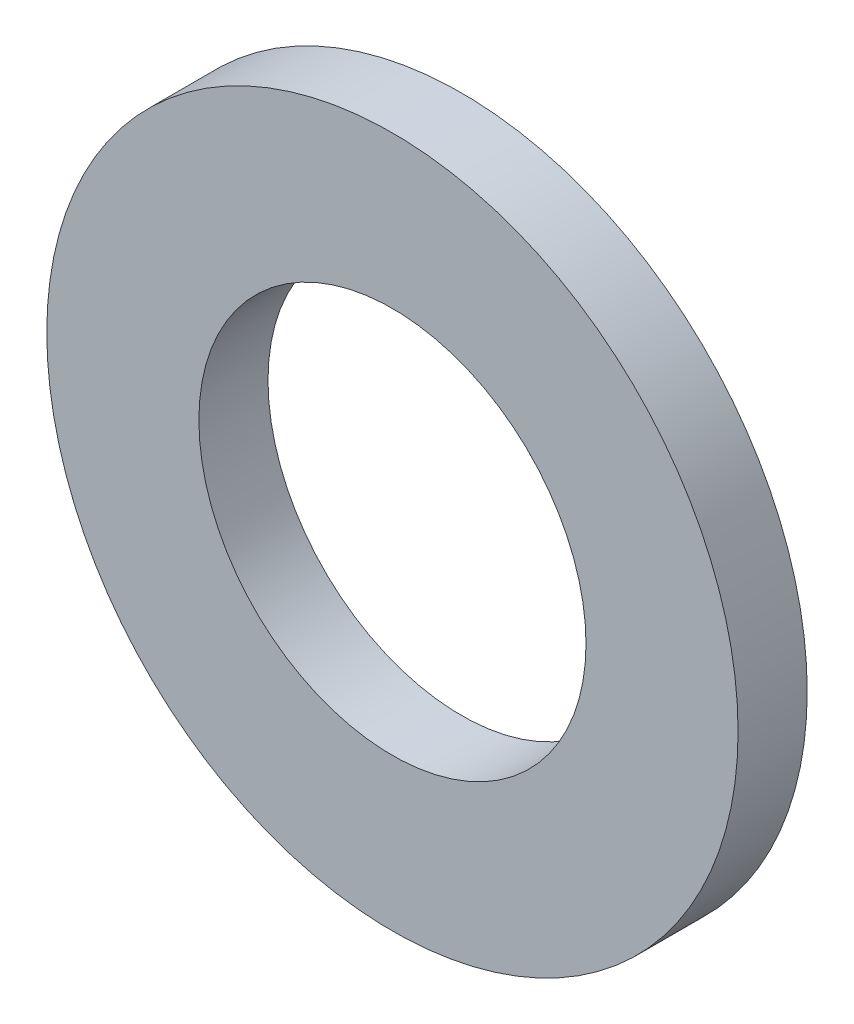
SolidWorks part; units mm, degrees
material "AISI 1035 鋼 (SS)"
ref_plane "前基準面" through (0, 0, 0) normal (0, 0, 1) x (1, 0, 0)
ref_plane "上基準面" through (0, 0, 0) normal (0, 1, 0) x (1, 0, 0)
ref_plane "右基準面" through (0, 0, 0) normal (1, 0, 0) x (0, 0, -1)
sketch "草圖1" plane through (0, 0, 0) normal (0, 0, 1) x (1, 0, 0)
  circle A0 centre (0, 0) radius 5
  circle A1 centre (0, 0) radius 2.8
  dimension "D1" = 5.6
  dimension "D2" = 10
extrude "填料-伸長1" add sketch "草圖1" along normal blind 1
